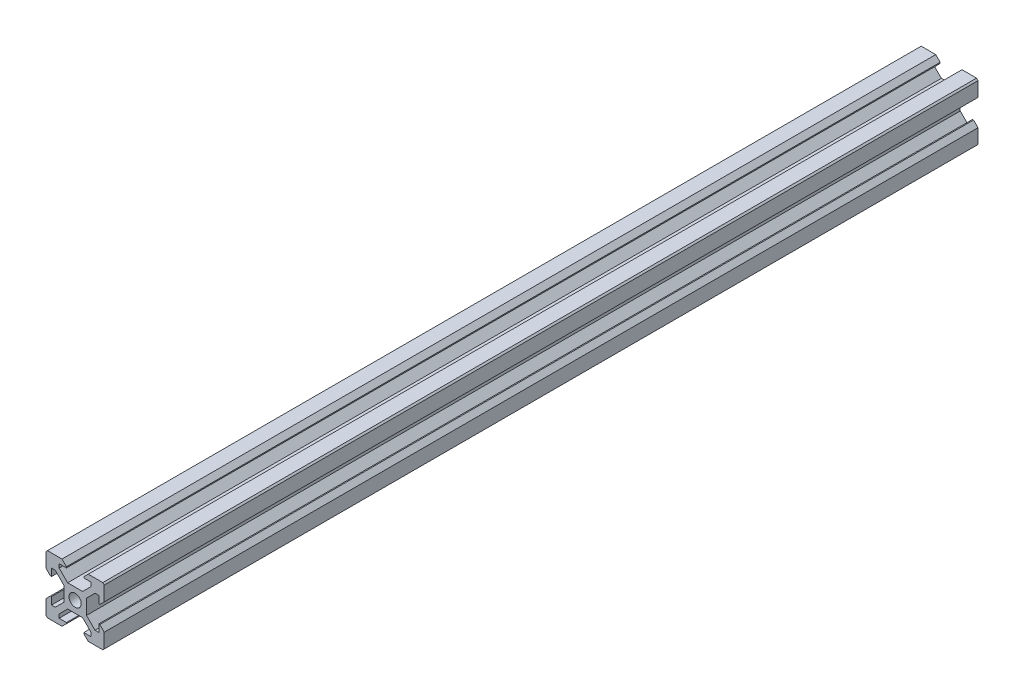
SolidWorks part; units mm, degrees
ref_plane "Front Plane" through (0, 0, 0) normal (0, 0, 1) x (1, 0, 0)
ref_plane "Top Plane" through (0, 0, 0) normal (0, 1, 0) x (1, 0, 0)
ref_plane "Right Plane" through (0, 0, 0) normal (1, 0, 0) x (0, 0, -1)
sketch "Sketch1" plane through (0, 0, 0) normal (0, 0, 1) x (1, 0, 0)
  line L0 (15.6876, 55.3211) -> (115.0437, 55.3211) construction
  line L1 (5.5, 6.8294) -> (2.5706, 3.9)
  line L2 (0, 3.9) -> (0, 2.1)
  line L3 (10, 10) -> (1.4849, 1.4849)
  line L4 (10, 10) -> (4.5, 10)
  line L5 (1.4849, 1.4849) -> (3.9, 3.9) construction
  line L6 (10, -10) -> (-10, 10) construction
  line L7 (10, 10) -> (1.4849, 1.4849) construction
  line L8 (0, 0) -> (-10, -10) construction
  line L10 (0, 3.9) -> (2.5706, 3.9)
  line L12 (-3.9, -3.9) -> (0, 0) construction
  line L13 (-3.9, 3.9) -> (3.9, -3.9) construction
  line L14 (5.5, 6.8294) -> (5.5, 8.12)
  line L15 (5.5, 8.12) -> (2.62, 8.12)
  line L16 (2.62, 8.12) -> (4.5, 10)
  line L17 (0, 2.1) -> (0, 16.7618) construction
  arc A0 (1.4849, 1.4849) -> (0, 2.1) centre (0, 0) ccw
  point P2 (0, 0)
  point P7 (0, 0)
  dimension "D3" = 45
  dimension "D4" = 6.1
  dimension "D8" = 4.2
  dimension "D1" = 20
  dimension "D2" = 11
  dimension "D5" = 1.88
  dimension "D6" = 9
  dimension "D7" = 0.94
  dimension "D9" = 3.9
extrude "Boss-Extrude1" add sketch "Sketch1" along normal blind 300
chamfer "Chamfer2" distance 0.5 angle 45 1 edges at (2.62, 8.12, 150)
mirror "Mirror1" about plane through (10, 10, 300) normal (-0.7071, 0.7071, 0) of bodies 102
chamfer "Chamfer1" distance 0.5 angle 45 1 edges at (10, 10, 150)
mirror "Mirror4" about plane through (0, 3.9, 300) normal (1, 0, 0) of bodies 103 104
mirror "Mirror5" about plane through (-3.9, 0, 300) normal (0, 1, 0) of bodies 105
